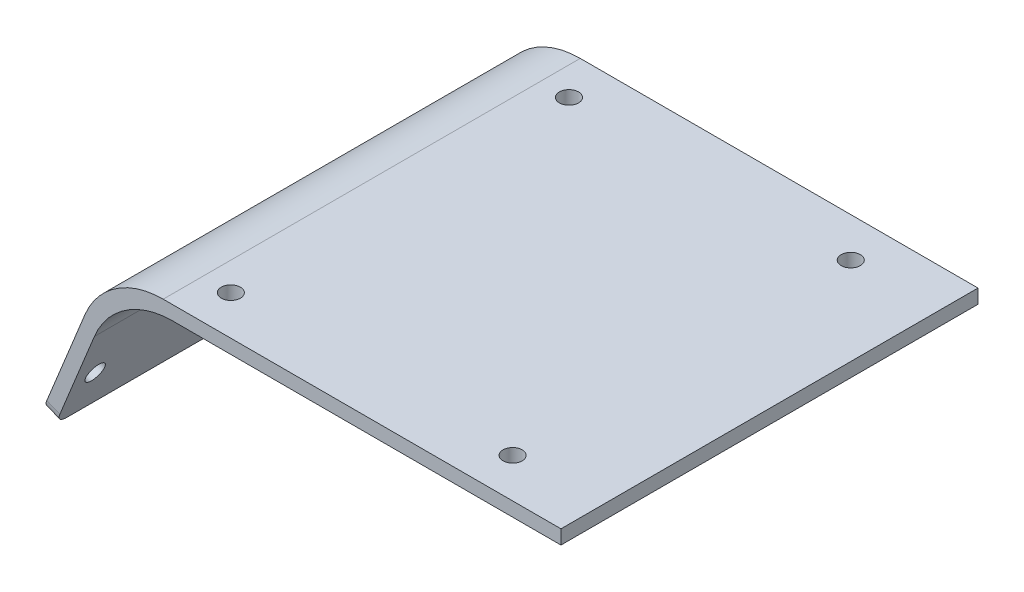
SolidWorks part; units mm, degrees
ref_plane "Piano frontale" through (0, 0, 0) normal (0, 0, 1) x (1, 0, 0)
ref_plane "Piano superiore" through (0, 0, 0) normal (0, 1, 0) x (1, 0, 0)
ref_plane "Piano destro" through (0, 0, 0) normal (1, 0, 0) x (0, 0, -1)
sketch "Schizzo2" plane through (0, 0, 0) normal (0, 0, 1) x (1, 0, 0)
  line L1 (-60, 40.8849) -> (20.66, 40.8849)
  line L9 (-69.0155, 12.1626) -> (-58.3198, 38.3849)
  line L10 (-58.3198, 38.3849) -> (20.66, 38.3849)
  line L12 (-71.3303, 13.1068) -> (-69.0155, 12.1626)
  line L21 (-71.3303, 13.1068) -> (-60, 40.8849)
  line L22 (-58.3198, 38.3849) -> (56, 38.3849) construction
  line L23 (58.5, 40.8849) -> (58.5, -38.4963) construction
  line L24 (56, 38.3849) -> (56, -38.4963) construction
  line L25 (20.66, 38.3849) -> (20.66, 40.8849)
  line L27 (-60, 40.8849) -> (58.5, 40.8849) construction
  dimension "D1" = 2.5
  dimension "D2" = 80.66
  dimension "D3" = 28.3198
extrude "Estrusione-Estrusione2" add sketch "Schizzo2" along normal blind 74
fillet "Raccordo3" radius 15 2 edges at (-60, 40.8849, 37) (-58.3198, 38.3849, 37)
fillet "Raccordo4" radius 2 2 edges at (-70.1729, 12.6347, 0) (-70.1729, 12.6347, 74)
sketch "Schizzo5" [suppressed] plane through (0, 40.8849, 0) normal (0, 1, 0) x (1, 0, 0)
  line L1 (50.0815, -80) -> (-49.9185, -80)
  line L2 (50.0815, -80) -> (50.0815, 0)
  line L3 (50.0815, 0) -> (-49.9185, 0)
  line L4 (-49.9185, -80) -> (-49.9185, 0)
  dimension "D1" = 100
  dimension "D2" = 80
ref_plane "Piano1" through (0, 40.8849, 0) normal (0, 1, 0) x (1, 0, 0)
sketch "Schizzo10" plane through (0, 40.8849, 0) normal (0, 1, 0) x (1, 0, 0)
  line L0 (20.66, -74) -> (-49.9185, -74) construction
  line L1 (-49.9185, 0) -> (-49.9185, -74) construction
  line L3 (-22.4185, -74) -> (-22.4185, 0) construction
  circle A2 centre (5.0815, -67) radius 1.7
  circle A3 centre (5.0815, -7) radius 1.7
  circle A6 centre (-44.9185, -67) radius 1.7
  circle A8 centre (-44.9185, -7) radius 1.7
  dimension "D3" = 3.4
  dimension "D4" = 3.4
  dimension "D5" = 3.4
  dimension "D6" = 3.4
  dimension "D1" = 7
  dimension "D2" = 5
  dimension "D7" = 27.5
extrude "Taglio-Estrusione1" cut sketch "Schizzo10" against normal blind 10
ref_plane "Piano2" through (0, 40.8849, 0) normal (0, 1, 0) x (1, 0, 0)
sketch "Schizzo13" plane through (-65.7392, 26.8142, 0) normal (-0.9259, 0.3777, 0) x (0, 0, 1)
  line L0 (0, 5.1146) -> (0, -12.8039) construction
  line L1 (72, -14.8039) -> (2, -14.8039) construction
  line L2 (37, 5.1146) -> (37, -14.8039) construction
  line L3 (74, 5.1146) -> (0, 5.1146) construction
  circle A0 centre (4, -6.8039) radius 1.7
  circle A1 centre (70, -6.8039) radius 1.7
  circle A2 centre (35, -6.8039) radius 1.7
  dimension "D1" = 3.4
  dimension "D4" = 3.4
  dimension "D6" = 8
  dimension "D2" = 4
  dimension "D3" = 8
  dimension "D5" = 35
extrude "Taglio-Estrusione3" cut sketch "Schizzo13" against normal through all both and the other way through all
